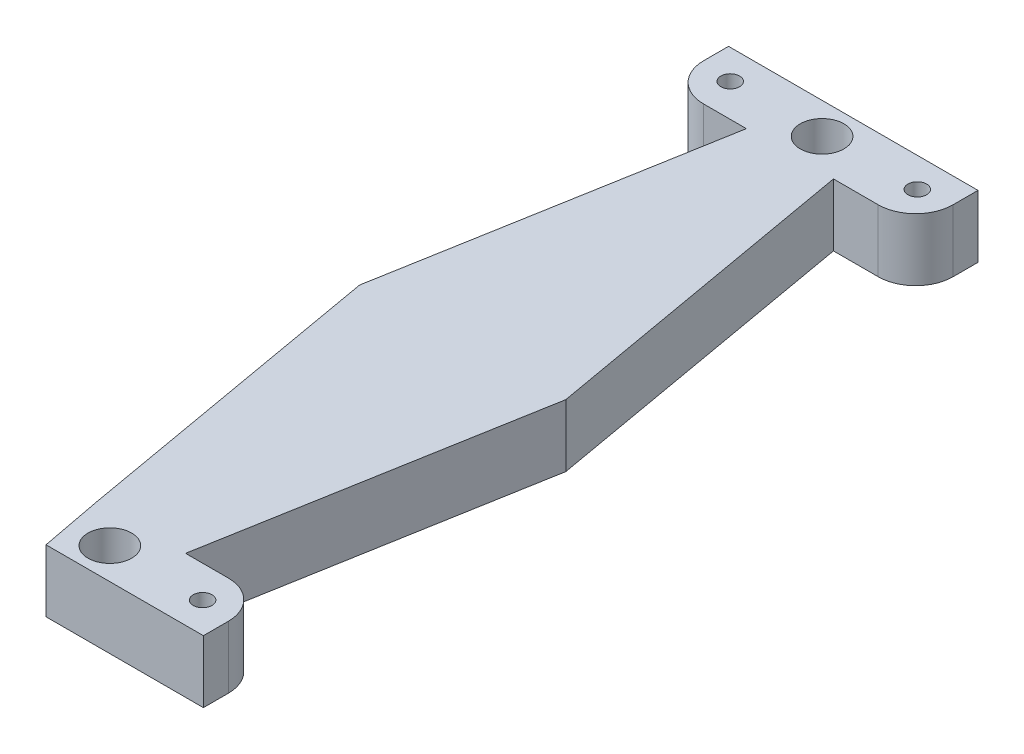
SolidWorks part; units mm, degrees
ref_plane "Front Plane" through (0, 0, 0) normal (0, 0, 1) x (1, 0, 0)
ref_plane "Top Plane" through (0, 0, 0) normal (0, 1, 0) x (1, 0, 0)
ref_plane "Right Plane" through (0, 0, 0) normal (1, 0, 0) x (0, 0, -1)
sketch "Sketch2" plane through (0, 0, 0) normal (0, 1, 0) x (1, 0, 0)
  line L0 (13.1286, 113.9396) -> (27.0894, 113.9396)
  line L1 (0, 0) -> (40, 0)
  line L2 (0, 0) -> (0, 10)
  line L3 (0, 10) -> (40, 10)
  line L4 (40, 0) -> (40, 10)
  line L5 (12.8623, 10) -> (27.1377, 10)
  line L8 (0.2662, 113.9396) -> (40.2662, 113.9396)
  line L9 (0.2662, 113.9396) -> (0.2662, 123.9396)
  line L10 (0.2662, 123.9396) -> (40.2662, 123.9396)
  line L11 (40.2662, 113.9396) -> (40.2662, 123.9396)
  line L13 (13.1286, 113.9396) -> (3.8318, 61.2148)
  line L14 (3.8318, 61.2148) -> (12.8623, 10)
  line L15 (27.1377, 10) -> (36.2772, 61.8329)
  line L16 (36.2772, 61.8329) -> (27.0894, 113.9396)
  circle A0 centre (20, 5) radius 3.5
  circle A1 centre (5, 4.8743) radius 1.5
  circle A2 centre (35, 4.8743) radius 1.5
  circle A3 centre (20.2662, 118.9396) radius 3.5
  circle A4 centre (35.2662, 119.2066) radius 1.5
  circle A5 centre (5.2662, 119.2066) radius 1.5
  dimension "D9" = 3
  dimension "D10" = 3
  dimension "D11" = 7
  dimension "D12" = 3
  dimension "D13" = 3
  dimension "D14" = 7
  dimension "D15" = 5
  dimension "D17" = 15
  dimension "D18" = 20
  dimension "D20" = 15
  dimension "D21" = 15
  dimension "D22" = 15
  dimension "D1" = 40
  dimension "D2" = 10
  dimension "D3" = 100
  dimension "D4" = 100
  dimension "D5" = 40
  dimension "D6" = 10
  dimension "D7" = 100
  dimension "D8" = 100
  dimension "D16" = 5
  dimension "D19" = 20
extrude "Boss-Extrude1" add sketch "Sketch2" along normal blind 10 contours L15 L16 L0 L13 L14 L3 | L8 L11 L10 L9 L0 A5 A4 A3 | L1 L4 L3 L2 A2 A1 A0
fillet "Fillet1" radius 6 4 edges at (40, 5, -10) (0, 5, -10) (0.2662, 5, -113.9396) (40.2662, 5, -113.9396)
sketch "Sketch3" plane through (0, 10, 0) normal (0, 1, 0) x (1, 0, 0)
  line L1 (3.8318, 61.2148) -> (14.762, 0)
  line L2 (0, 0) -> (40, 0) construction
  line L3 (36.2772, 61.8329) -> (25.1787, 0)
  line L4 (25.1787, 0) -> (14.762, 0)
  line L5 (3.8318, 61.2148) -> (36.2772, 61.8329)
  line L6 (14.762, 0) -> (0, 0)
  line L7 (0, 0) -> (0, 10.1347)
  line L8 (0, 10.1347) -> (12.8623, 10)
  line L9 (12.8623, 10) -> (14.762, 0)
  point P9 (0, 0)
extrude "Cut-Extrude2" cut sketch "Sketch3" against normal through all contours L6 L7 L8 L9
sketch "Sketch4" plane through (0, 10, 0) normal (0, 1, 0) x (1, 0, 0)
  line L0 (27.1377, 10) -> (25.5101, 0)
  line L1 (14.762, 0) -> (40, 0) construction
  line L2 (12.8623, 10) -> (14.762, 0) construction
  line L3 (25.5101, 0) -> (42.4529, 0)
  line L4 (42.4529, 0) -> (42.4529, 10)
  line L5 (42.4529, 10) -> (27.1377, 10)
  dimension "D1" = 20
